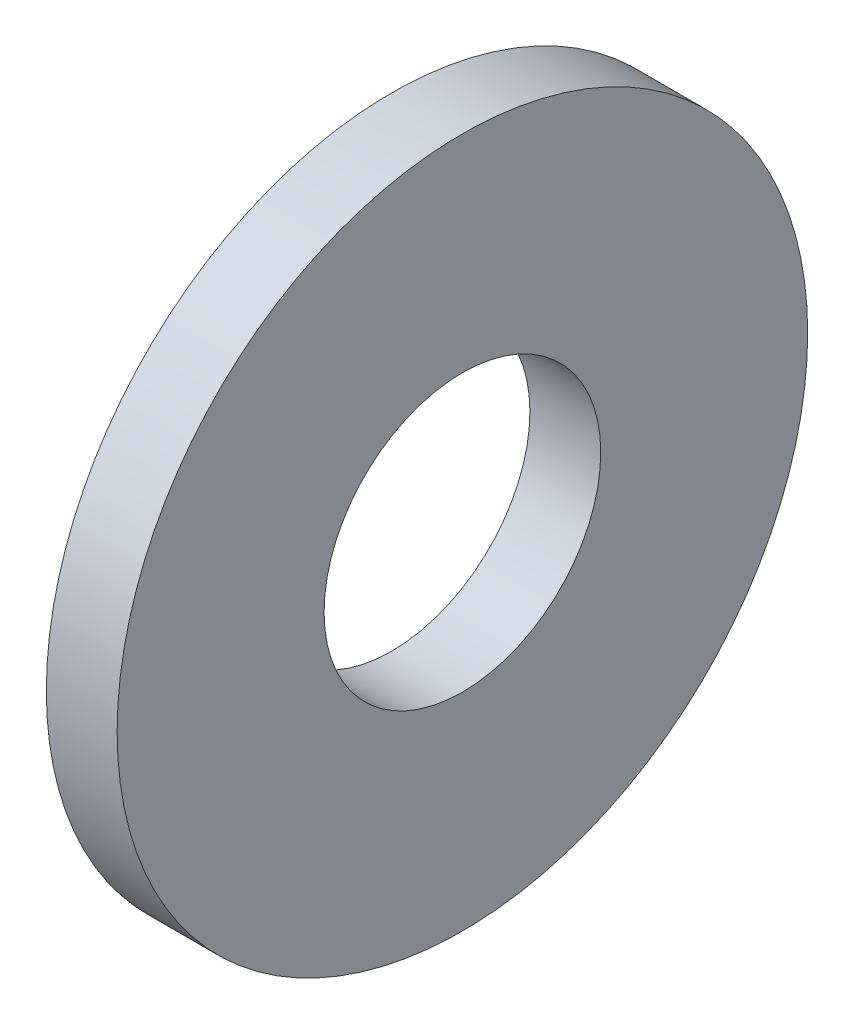
SolidWorks part; units mm, degrees
ref_plane "Plane1" through (0, 0, 0) normal (0, 0, 1) x (1, 0, 0)
ref_plane "Plane2" through (0, 0, 0) normal (0, 1, 0) x (1, 0, 0)
ref_plane "Plane3" through (0, 0, 0) normal (1, 0, 0) x (0, 0, -1)
sketch "Sketch1" plane through (0, 0, 0) normal (0, 0, 1) x (1, 0, 0)
  line L0 (-34.925, 0) -> (9.525, 0) construction
  line L1 (0, 1.5875) -> (0, 3.9624)
  line L2 (0, 3.9624) -> (-0.8128, 3.9624)
  line L3 (-0.8128, 3.9624) -> (-0.8128, 1.5875)
  line L4 (-0.8128, 1.5875) -> (0, 1.5875)
  dimension "Thickness" = 0.8128
  dimension "Inside_dia" = 3.175
  dimension "Outside_dia" = 7.9248
revolve "Base-Revolve" add sketch "Sketch1" angle 360 about L0
